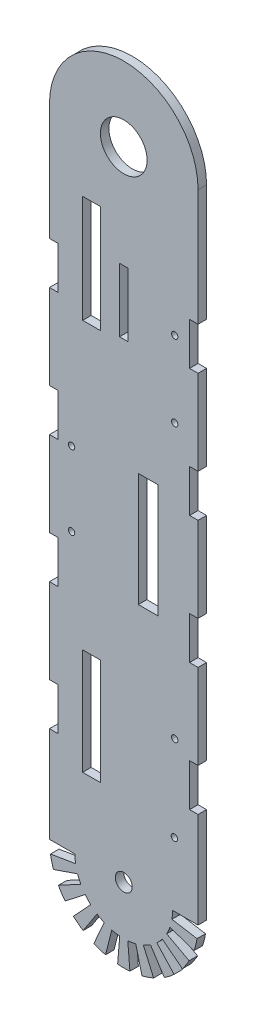
SolidWorks part; units mm, degrees
material "1060 Alloy"
ref_plane "Front Plane" through (0, 0, 0) normal (0, 0, 1) x (1, 0, 0)
ref_plane "Top Plane" through (0, 0, 0) normal (0, 1, 0) x (1, 0, 0)
ref_plane "Right Plane" through (0, 0, 0) normal (1, 0, 0) x (0, 0, -1)
sketch "Sketch1" plane through (0, 0, 0) normal (0, 0, 1) x (1, 0, 0)
  line L0 (-35, 300) -> (-35, 245.1193)
  line L1 (0, 300) -> (0, 0) construction
  line L2 (-35, 245.1193) -> (-31, 245.1193)
  line L3 (-31, 245.1193) -> (-31, 225.1193)
  line L4 (-31, 225.1193) -> (-35, 225.1193)
  line L5 (-35, 185.1193) -> (-31, 185.1193)
  line L6 (-31, 185.1193) -> (-31, 165.1193)
  line L7 (-31, 165.1193) -> (-35, 165.1193)
  line L8 (-35, 125.1193) -> (-31, 125.1193)
  line L9 (-31, 125.1193) -> (-31, 105.1193)
  line L10 (-31, 105.1193) -> (-35, 105.1193)
  line L11 (-35, 65.1193) -> (-31, 65.1193)
  line L12 (-31, 65.1193) -> (-31, 45.1193)
  line L13 (-31, 45.1193) -> (-35, 45.1193)
  line L14 (-35, 225.1193) -> (-35, 185.1193)
  line L15 (-35, 165.1193) -> (-35, 125.1193)
  line L16 (-35, 105.1193) -> (-35, 65.1193)
  line L17 (-35, 45.1193) -> (-35, 0)
  line L18 (35, 300) -> (35, 245.1193)
  line L19 (35, 45.1193) -> (35, 0)
  line L20 (35, 105.1193) -> (35, 65.1193)
  line L21 (35, 165.1193) -> (35, 125.1193)
  line L22 (35, 225.1193) -> (35, 185.1193)
  line L23 (31, 45.1193) -> (35, 45.1193)
  line L24 (31, 65.1193) -> (31, 45.1193)
  line L25 (35, 65.1193) -> (31, 65.1193)
  line L26 (31, 105.1193) -> (35, 105.1193)
  line L27 (31, 125.1193) -> (31, 105.1193)
  line L28 (35, 125.1193) -> (31, 125.1193)
  line L29 (31, 165.1193) -> (35, 165.1193)
  line L30 (31, 185.1193) -> (31, 165.1193)
  line L31 (35, 185.1193) -> (31, 185.1193)
  line L32 (31, 225.1193) -> (35, 225.1193)
  line L33 (31, 245.1193) -> (31, 225.1193)
  line L34 (35, 245.1193) -> (31, 245.1193)
  line L35 (2, 251.5) -> (-2, 251.5)
  line L36 (-19.3587, 270.1244) -> (-10.8433, 270.1244)
  line L37 (-19.3587, 270.1244) -> (-19.3587, 219.5326)
  line L38 (-19.3587, 219.5326) -> (-10.8433, 219.5326)
  line L39 (-10.8433, 270.1244) -> (-10.8433, 219.5326)
  line L40 (6.8594, 170.2051) -> (16.2232, 170.2051)
  line L41 (6.8594, 170.2051) -> (6.8594, 116.6977)
  line L42 (6.8594, 116.6977) -> (16.2232, 116.6977)
  line L43 (16.2232, 170.2051) -> (16.2232, 116.6977)
  line L44 (-19.3587, 85.1193) -> (-10.8433, 85.1193)
  line L45 (-19.3587, 85.1193) -> (-19.3587, 35.1473)
  line L46 (-19.3587, 35.1473) -> (-10.8433, 35.1473)
  line L47 (-10.8433, 85.1193) -> (-10.8433, 35.1473)
  line L48 (-2, 251.5) -> (-2, 221.5)
  line L49 (-2, 221.5) -> (2, 221.5)
  line L50 (2, 221.5) -> (2, 251.5)
  line L67 (-23, 0) -> (-35, 0)
  line L68 (-22.6863, -3.7857) -> (-34.5226, -5.7608)
  line L69 (-21.7538, -7.4681) -> (-33.1036, -11.3645)
  line L70 (-20.2279, -10.9468) -> (-30.7816, -16.6582)
  line L71 (-18.1502, -14.1269) -> (-27.6199, -21.4974)
  line L72 (-15.5775, -16.9216) -> (-23.7049, -25.7503)
  line L73 (-12.5798, -19.2548) -> (-19.1432, -29.3008)
  line L74 (-9.239, -21.0628) -> (-14.0593, -32.0521)
  line L75 (-5.6462, -22.2962) -> (-8.592, -33.929)
  line L76 (-1.8993, -22.9214) -> (-2.8903, -34.8805)
  line L77 (1.8993, -22.9214) -> (2.8903, -34.8805)
  line L78 (5.6462, -22.2962) -> (8.592, -33.929)
  line L79 (9.239, -21.0628) -> (14.0593, -32.0521)
  line L80 (12.5798, -19.2548) -> (19.1432, -29.3008)
  line L81 (15.5775, -16.9216) -> (23.7049, -25.7503)
  line L82 (18.1502, -14.1269) -> (27.6199, -21.4974)
  line L83 (20.2279, -10.9468) -> (30.7816, -16.6582)
  line L84 (21.7538, -7.4681) -> (33.1036, -11.3645)
  line L85 (22.6863, -3.7857) -> (34.5226, -5.7608)
  line L86 (23, 0) -> (35, 0)
  arc A0 (-34.5226, -5.7608) -> (-33.1036, -11.3645) centre (0, 0) ccw
  circle A1 centre (0, 0) radius 4
  circle A2 centre (0, 300) radius 11
  arc A3 (35, 300) -> (-35, 300) centre (0, 300) ccw
  circle A4 centre (23.9967, 235.0913) radius 1.5
  circle A5 centre (-24.5759, 165.7122) radius 1.5
  circle A6 centre (23.9967, 199.3846) radius 1.5
  circle A7 centre (-24.5759, 130.7419) radius 1.5
  circle A8 centre (23.9967, 70.5174) radius 1.5
  circle A9 centre (23.8341, 30.1439) radius 1.5
  arc A10 (-23, 0) -> (-22.6863, -3.7857) centre (0, 0) ccw
  arc A11 (33.1036, -11.3645) -> (34.5226, -5.7608) centre (0, 0) ccw
  arc A12 (22.6863, -3.7857) -> (23, 0) centre (0, 0) ccw
  arc A13 (20.2279, -10.9468) -> (21.7538, -7.4681) centre (0, 0) ccw
  arc A14 (27.6199, -21.4974) -> (30.7816, -16.6582) centre (0, 0) ccw
  arc A15 (15.5775, -16.9216) -> (18.1502, -14.1269) centre (0, 0) ccw
  arc A16 (19.1432, -29.3008) -> (23.7049, -25.7503) centre (0, 0) ccw
  arc A17 (9.239, -21.0628) -> (12.5798, -19.2548) centre (0, 0) ccw
  arc A18 (8.592, -33.929) -> (14.0593, -32.0521) centre (0, 0) ccw
  arc A19 (1.8993, -22.9214) -> (5.6462, -22.2962) centre (0, 0) ccw
  arc A20 (-2.8903, -34.8805) -> (2.8903, -34.8805) centre (0, 0) ccw
  arc A21 (-5.6462, -22.2962) -> (-1.8993, -22.9214) centre (0, 0) ccw
  arc A22 (-14.0593, -32.0521) -> (-8.592, -33.929) centre (0, 0) ccw
  arc A23 (-12.5798, -19.2548) -> (-9.239, -21.0628) centre (0, 0) ccw
  arc A24 (-23.7049, -25.7503) -> (-19.1432, -29.3008) centre (0, 0) ccw
  arc A25 (-18.1502, -14.1269) -> (-15.5775, -16.9216) centre (0, 0) ccw
  arc A26 (-30.7816, -16.6582) -> (-27.6199, -21.4974) centre (0, 0) ccw
  arc A27 (-21.7538, -7.4681) -> (-20.2279, -10.9468) centre (0, 0) ccw
  circle A28 centre (0, 300) radius 18.5 construction
  point P87 (0, 251.5)
  point P88 (0, 0)
  dimension "D1" = 300
  dimension "D2" = 35
  dimension "D3" = 35
  dimension "D4" = 22
  dimension "D5" = 8
  dimension "D6" = 4
  dimension "D11" = 48.5
  dimension "D7" = 20
  dimension "D8" = 40
  dimension "D9" = 40
  dimension "D10" = 40
  dimension "D12" = 30
extrude "Boss-Extrude1" add sketch "Sketch1" along normal blind 4
